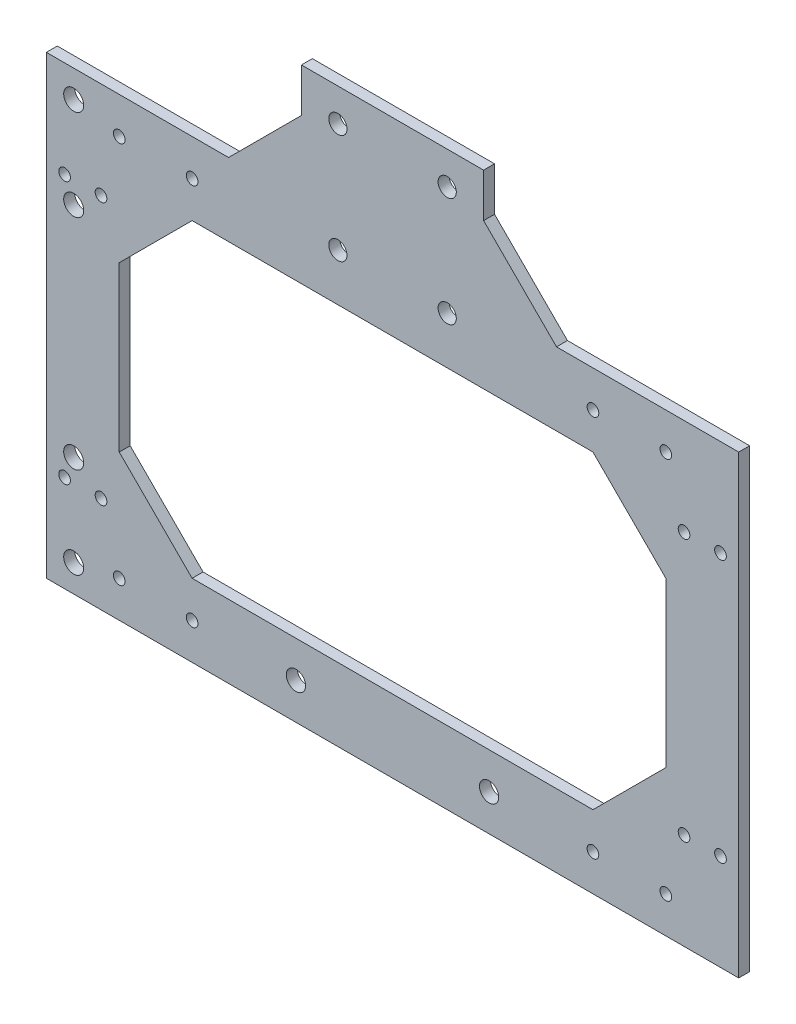
SolidWorks part; units mm, degrees
material "Thornel Mat VMA"
ref_plane "Front Plane" through (0, 0, 0) normal (0, 0, 1) x (1, 0, 0)
ref_plane "Top Plane" through (0, 0, 0) normal (0, 1, 0) x (1, 0, 0)
ref_plane "Right Plane" through (0, 0, 0) normal (1, 0, 0) x (0, 0, -1)
sketch "Sketch1" plane through (0, 0, 0) normal (0, 0, 1) x (1, 0, 0)
  line L1 (-25, 44.5) -> (-25, 91.5) construction
  line L3 (25, 91.5) -> (25, 44.5) construction
  line L4 (95, -62.5) -> (95, 62.5)
  line L5 (95, 62.5) -> (-95, 62.5)
  line L6 (-95, 62.5) -> (-95, -62.5)
  line L7 (-95, -62.5) -> (95, -62.5)
  line L8 (95, -62.5) -> (95, 62.5)
  line L9 (95, 62.5) -> (45, 62.5)
  line L10 (-95, 62.5) -> (-95, -62.5)
  line L11 (-95, -62.5) -> (95, -62.5)
  line L12 (-25, 94.5) -> (-25, 74.5)
  line L13 (-25, 74.5) -> (25, 74.5)
  line L14 (25, 74.5) -> (25, 94.5)
  line L15 (25, 94.5) -> (-25, 94.5)
  line L16 (-25, 94.5) -> (-25, 82.5)
  line L18 (25, 82.5) -> (25, 94.5)
  line L19 (25, 94.5) -> (-25, 94.5)
  line L20 (-45, 62.5) -> (-95, 62.5)
  line L21 (75, -42.5) -> (75, 42.5) construction
  line L22 (-75, -42.5) -> (75, -42.5) construction
  line L23 (-75, 42.5) -> (-75, -42.5) construction
  line L24 (75, 42.5) -> (-75, 42.5) construction
  line L25 (75, -22.5) -> (75, 22.5)
  line L26 (-55, -42.5) -> (55, -42.5)
  line L27 (-75, 22.5) -> (-75, -22.5)
  line L28 (55, 42.5) -> (-55, 42.5)
  line L29 (-55, 42.5) -> (-75, 22.5)
  line L30 (-75, -22.5) -> (-55, -42.5)
  line L31 (75, 22.5) -> (55, 42.5)
  line L32 (55, -42.5) -> (75, -22.5)
  line L33 (-25, 82.5) -> (-45, 62.5)
  line L34 (45, 62.5) -> (25, 82.5)
  line L35 (-95, 52.5) -> (95, 52.5) construction
  line L36 (-95, 0) -> (95, 0) construction
  line L37 (0, 61.2) -> (0, 42.5) construction
  circle A0 centre (15, 85.5) radius 2.5 construction
  circle A1 centre (-15, 85.5) radius 2.5 construction
  circle A2 centre (15, 85.5) radius 2.5
  circle A3 centre (-15, 85.5) radius 2.5
  circle A4 centre (-15, 55.5) radius 2.5
  circle A5 centre (15, 55.5) radius 2.5
  circle A6 centre (-75, 52.5) radius 1.6
  circle A7 centre (-55, 52.5) radius 1.6
  circle A8 centre (75, 52.5) radius 1.6
  circle A9 centre (55, 52.5) radius 1.6
  circle A10 centre (75, -52.5) radius 1.6
  circle A11 centre (55, -52.5) radius 1.6
  circle A12 centre (-55, -52.5) radius 1.6
  circle A13 centre (-75, -52.5) radius 1.6
  circle A14 centre (-26.5, -52.5) radius 2.65
  circle A15 centre (26.5, -52.5) radius 2.65
  point P6 (25, 62.5)
  point P8 (-25, 62.5)
  dimension "D4" = 3.2
  dimension "D5" = 20
  dimension "D6" = 20
  dimension "D7" = 5.3
  dimension "D3" = 10
  dimension "D1" = 0
  dimension "D2" = 0
extrude "Extrude1" add sketch "Sketch1" along normal blind 3
sketch "Sketch2" plane through (0, 0, 3) normal (0, 0, 1) x (1, 0, 0)
  arc A0 (90, -37.6) -> (90, -34.4) centre (90, -36) ccw construction
  arc A1 (90, -34.4) -> (90, -37.6) centre (90, -36) ccw construction
  arc A2 (80, -37.6) -> (80, -34.4) centre (80, -36) ccw construction
  arc A3 (80, -34.4) -> (80, -37.6) centre (80, -36) ccw construction
  arc A4 (90, 34.4) -> (90, 37.6) centre (90, 36) ccw construction
  arc A5 (90, 37.6) -> (90, 34.4) centre (90, 36) ccw construction
  arc A6 (80, 34.4) -> (80, 37.6) centre (80, 36) ccw construction
  arc A7 (80, 37.6) -> (80, 34.4) centre (80, 36) ccw construction
  arc A8 (90, -37.6) -> (90, -34.4) centre (90, -36) ccw
  arc A9 (90, -34.4) -> (90, -37.6) centre (90, -36) ccw
  arc A10 (80, -37.6) -> (80, -34.4) centre (80, -36) ccw
  arc A11 (80, -34.4) -> (80, -37.6) centre (80, -36) ccw
  arc A12 (90, 34.4) -> (90, 37.6) centre (90, 36) ccw
  arc A13 (90, 37.6) -> (90, 34.4) centre (90, 36) ccw
  arc A14 (80, 34.4) -> (80, 37.6) centre (80, 36) ccw
  arc A15 (80, 37.6) -> (80, 34.4) centre (80, 36) ccw
extrude "Cut-Extrude1" cut sketch "Sketch2" against normal blind 3
ref_plane "Plane1" through (-95, 44.5, -2) normal (-1, 0, 0) x (0, 0, 1)
sketch "Sketch4" plane through (0, 0, 3) normal (0, 0, 1) x (1, 0, 0)
  circle A0 centre (-80, -36) radius 1.6 construction
  circle A1 centre (-90, -36) radius 1.6 construction
  circle A2 centre (-80, 36) radius 1.6 construction
  circle A3 centre (-90, 36) radius 1.6 construction
  circle A4 centre (-80, -36) radius 1.6
  circle A5 centre (-90, -36) radius 1.6
  circle A6 centre (-80, 36) radius 1.6
  circle A7 centre (-90, 36) radius 1.6
extrude "Cut-Extrude2" cut sketch "Sketch4" against normal blind 26
sketch "Sketch5" plane through (0, 0, 3) normal (0, 0, 1) x (1, 0, 0)
  circle A0 centre (-87.5, -55) radius 2.75 construction
  circle A1 centre (-87.5, -30) radius 2.75 construction
  circle A2 centre (-87.5, 30) radius 2.75 construction
  circle A3 centre (-87.5, 55) radius 2.75 construction
  circle A4 centre (-87.5, -55) radius 2.75
  circle A5 centre (-87.5, -30) radius 2.75
  circle A6 centre (-87.5, 30) radius 2.75
  circle A7 centre (-87.5, 55) radius 2.75
extrude "Cut-Extrude3" cut sketch "Sketch5" against normal blind 10
